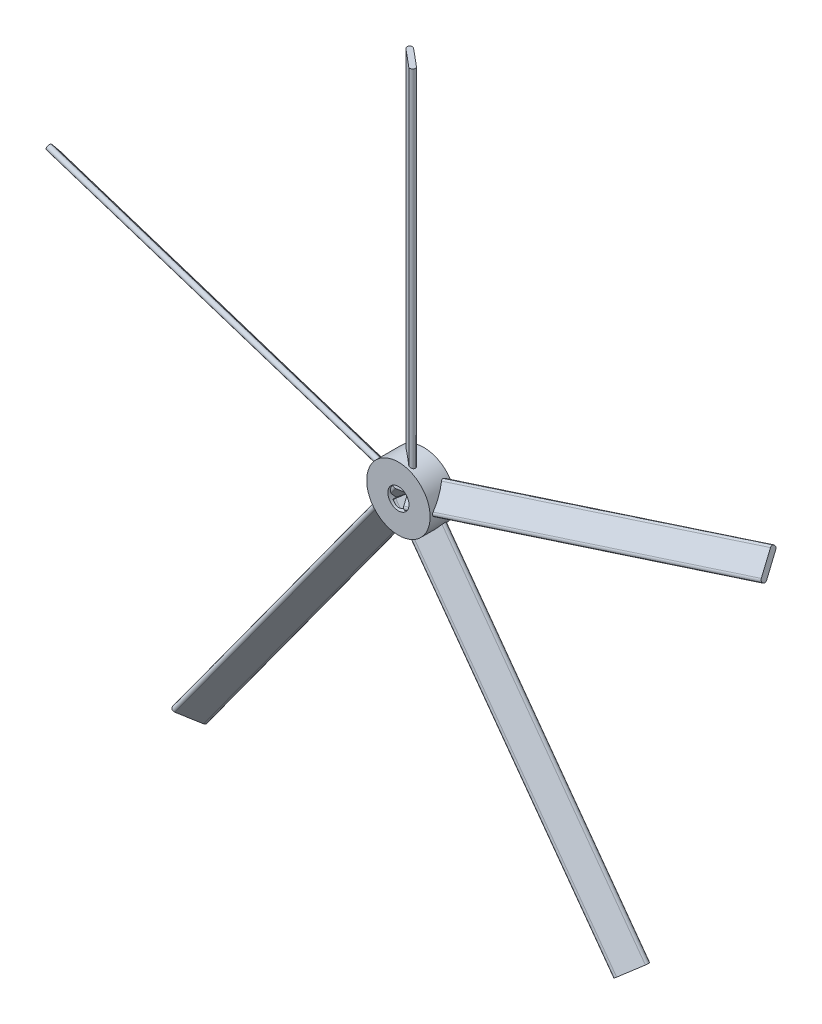
SolidWorks part; units mm, degrees
ref_plane "Front Plane" through (0, 0, 0) normal (0, 0, 1) x (1, 0, 0)
ref_plane "Top Plane" through (0, 0, 0) normal (0, 1, 0) x (1, 0, 0)
ref_plane "Right Plane" through (0, 0, 0) normal (1, 0, 0) x (0, 0, -1)
sketch "Sketch1" plane through (0, 0, 0) normal (0, 0, 1) x (1, 0, 0)
  circle A0 centre (0, 0) radius 2.5
  circle A1 centre (0, 0) radius 7.5
  dimension "D1" = 5
  dimension "D2" = 5
extrude "Boss-Extrude1" add sketch "Sketch1" along normal blind 6
sketch "Sketch3" plane through (0, 0, 0) normal (0, 1, 0) x (1, 0, 0)
  line L0 (-3.5914, 0) -> (3.5914, -6) construction
  line L1 (-7.5, -6) -> (7.5, -6) construction
  line L2 (0, 0) -> (0, -6) construction
  line L3 (-2.4276, -1.8106) -> (1.7106, -5.2674)
  line L4 (-1.6025, -0.8229) -> (2.5357, -4.2797)
  line L5 (7.5, 0) -> (-7.5, 0) construction
  arc A0 (-1.6025, -0.8229) -> (-2.4276, -1.8106) centre (-2.0151, -1.3168) ccw
  arc A1 (1.7106, -5.2674) -> (2.5357, -4.2797) centre (2.1232, -4.7735) ccw
  point P7 (0, -3)
  point P9 (2.3361, -4.7836)
  point P11 (0, 0)
  point P18 (2.1232, -4.7735)
extrude "Boss-Extrude2" add sketch "Sketch3" along normal blind 88.9
pattern_circular "CirPattern1" count 5 over 360 about axis through (0, 0, 0) along (0, 0, 1) of "Boss-Extrude2"
